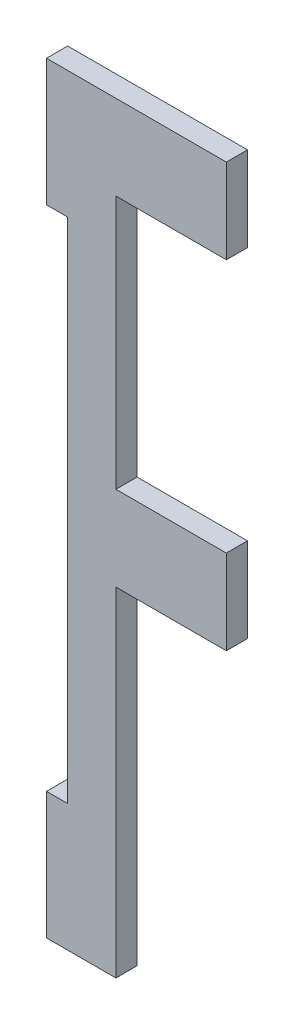
SolidWorks part; units mm, degrees
ref_plane "Front Plane" through (0, 0, 0) normal (0, 0, 1) x (1, 0, 0)
ref_plane "Top Plane" through (0, 0, 0) normal (0, 1, 0) x (1, 0, 0)
ref_plane "Right Plane" through (0, 0, 0) normal (1, 0, 0) x (0, 0, -1)
sketch "Sketch1" plane through (0, 0, 0) normal (0, 0, 1) x (1, 0, 0)
  line L0 (-3.175, -95.25) -> (7.239, -95.25)
  line L1 (7.239, -31.75) -> (23.8125, -31.75)
  line L2 (0, -76.2) -> (0, 0)
  line L3 (23.8125, -31.75) -> (23.8125, -44.45)
  line L4 (7.239, -95.25) -> (7.239, -44.45)
  line L5 (23.8125, -44.45) -> (7.239, -44.45)
  line L6 (7.239, 6.35) -> (7.239, -31.75)
  line L7 (-3.175, 19.05) -> (-3.175, 0)
  line L8 (-3.175, 0) -> (0, 0)
  line L9 (-3.175, 19.05) -> (23.8125, 19.05)
  line L10 (23.8125, 19.05) -> (23.8125, 6.35)
  line L11 (23.8125, 6.35) -> (7.239, 6.35)
  line L12 (0, -76.2) -> (-3.175, -76.2)
  line L13 (-3.175, -76.2) -> (-3.175, -95.25)
  point P0 (0, 0)
  dimension "D1" = 3.175
  dimension "D2" = 10.414
  dimension "D3" = 114.3
  dimension "D4" = 12.7
  dimension "D5" = 7.239
  dimension "D6" = 19.05
  dimension "D7" = 19.05
  dimension "D8" = 38.1
  dimension "D9" = 16.5735
extrude "Boss-Extrude1" add sketch "Sketch1" along normal blind 3.175
